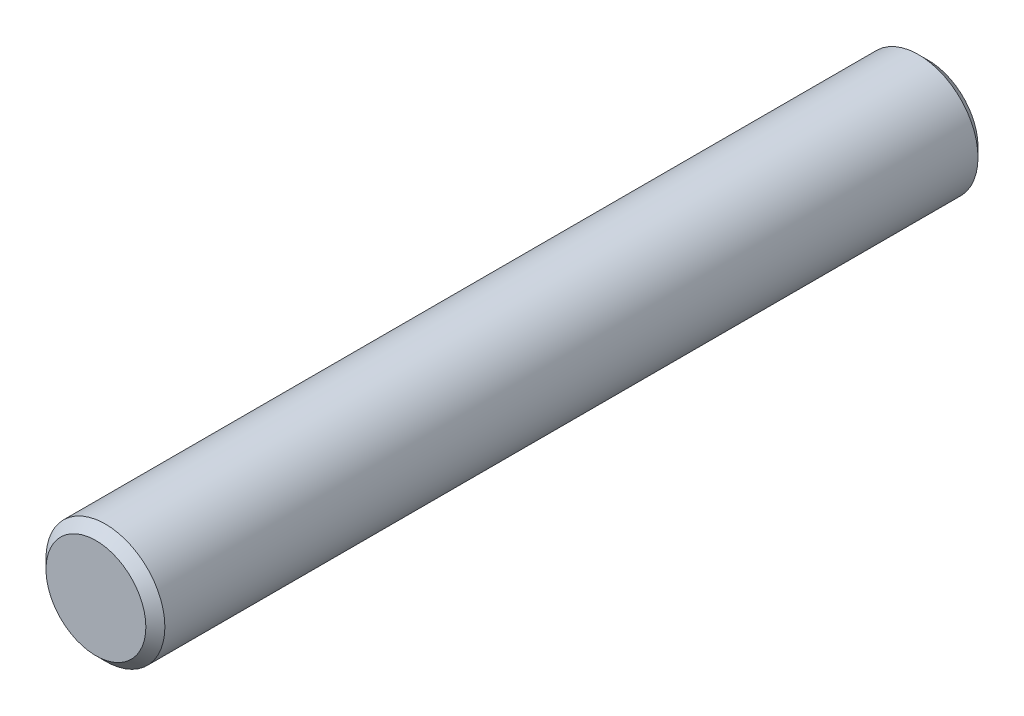
SolidWorks part; units mm, degrees
ref_plane "Front" through (0, 0, 0) normal (0, 0, 1) x (1, 0, 0)
ref_plane "Top" through (0, 0, 0) normal (0, 1, 0) x (1, 0, 0)
ref_plane "Right" through (0, 0, 0) normal (1, 0, 0) x (0, 0, -1)
sketch "Sketch1" plane through (0, 0, 0) normal (0, 0, 1) x (1, 0, 0)
  circle A0 centre (0, 0) radius 1.5875
  dimension "D1" = 3.175
extrude "Boss-Extrude1" add sketch "Sketch1" against normal blind 22.225
chamfer "Chamfer1" distance 0.254 angle 45 2 edges at (1.5875, 0, 0) (1.5875, 0, -22.225)
